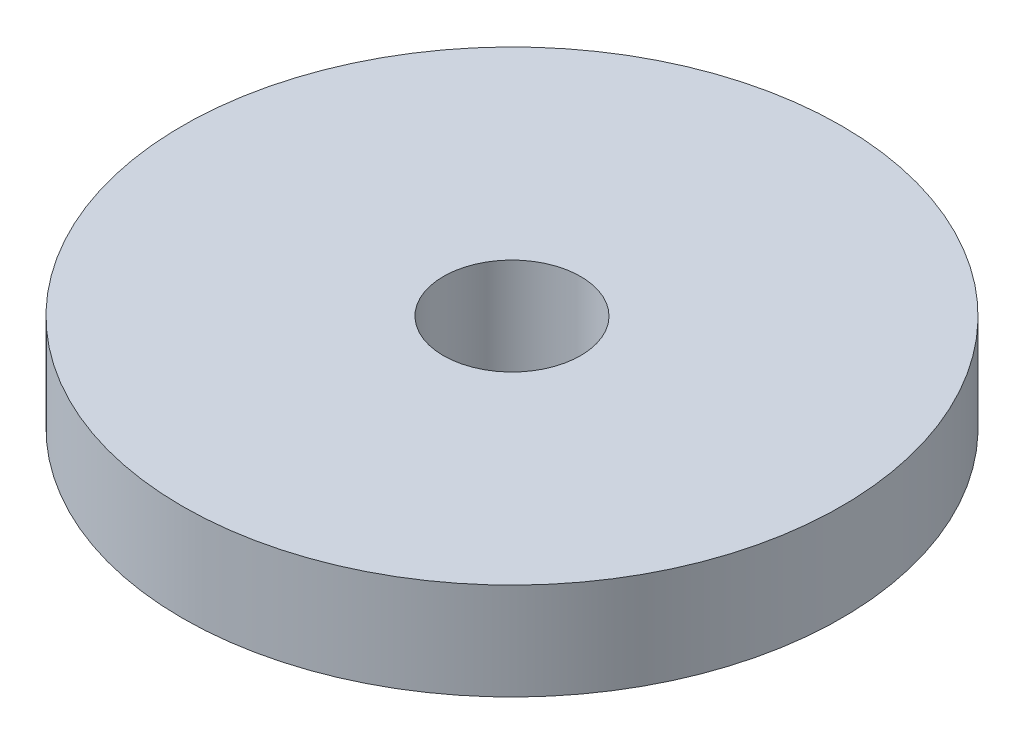
SolidWorks part; units mm, degrees
ref_plane "Front Plane" through (0, 0, 0) normal (0, 0, 1) x (1, 0, 0)
ref_plane "Top Plane" through (0, 0, 0) normal (0, 1, 0) x (1, 0, 0)
ref_plane "Right Plane" through (0, 0, 0) normal (1, 0, 0) x (0, 0, -1)
sketch "Sketch1" plane through (0, 0, 0) normal (0, 1, 0) x (1, 0, 0)
  circle A0 centre (0, 0) radius 10.795
  dimension "D1" = 21.59
extrude "Boss-Extrude1" add sketch "Sketch1" along normal blind 3.175
sketch "Sketch2" plane through (0, 3.175, 0) normal (0, 1, 0) x (1, 0, 0)
  point P0 (0, 0)
hole_wizard "#8 Clearance Hole1" positions "3DSketch1" profile "Sketch3" hole size "#8" standard "ANSI Inch"
sketch3d "3DSketch1"
  point P0 (0, 3.175, 0)
sketch "Sketch3" plane through (0, 3.175, 0) normal (1, 0, 0) x (0, 0, 1)
  line L0 (0, 0) -> (0, 11.5107)
  line L1 (0, 11.5107) -> (2.2479, 10.16)
  line L2 (2.2479, 10.16) -> (2.2479, 0)
  line L5 (2.2479, 0) -> (0, 0)
  line L10 (0, 11.5107) -> (-2.2479, 10.16) construction
  line L11 (0, -6.35) -> (0, 107.95) construction
  dimension "Hole Dia." = 4.4958
  dimension "Hole Depth" = 10.16
  dimension "Drill Angle" = 118
